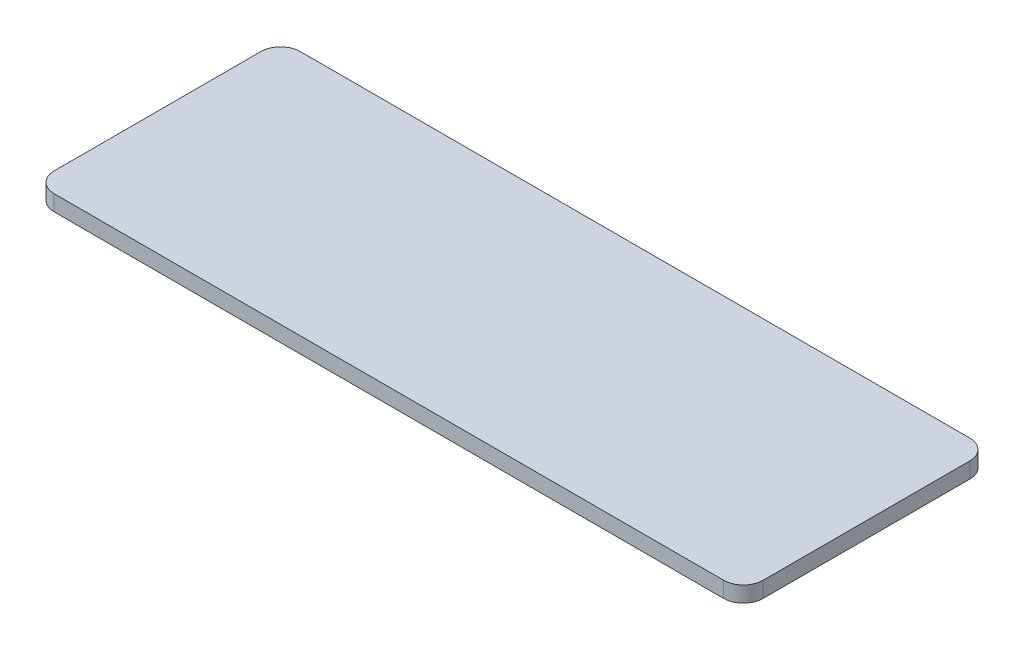
SolidWorks part; units mm, degrees
ref_plane "Front Plane" through (0, 0, 0) normal (0, 0, 1) x (1, 0, 0)
ref_plane "Top Plane" through (0, 0, 0) normal (0, 1, 0) x (1, 0, 0)
ref_plane "Right Plane" through (0, 0, 0) normal (1, 0, 0) x (0, 0, -1)
sketch "Sketch1" plane through (0, 0, 0) normal (0, 1, 0) x (1, 0, 0)
  line L1 (0, 0) -> (72, 0)
  line L2 (0, 0) -> (0, 25)
  line L3 (0, 25) -> (72, 25)
  line L4 (72, 0) -> (72, 25)
  dimension "D1" = 72
  dimension "D2" = 25
extrude "Boss-Extrude1" add sketch "Sketch1" along normal blind 1.6
fillet "Fillet1" radius 2 4 edges at (0, 0.8, 0) (0, 0.8, -25) (72, 0.8, -25) (72, 0.8, 0)
sketch "Sketch2" plane through (0, 1.6, 0) normal (0, 1, 0) x (1, 0, 0)
  line L0 (70, 25) -> (2, 25) construction
  line L1 (72, 2) -> (72, 23) construction
  circle A0 centre (64, 18) radius 0.1
  circle A1 centre (46, 18) radius 0.1
  circle A2 centre (28, 18) radius 0.1
  circle A3 centre (10, 18) radius 0.1
  point P0 (64, 18)
  dimension "D2" = 7
  dimension "D3" = 8
  dimension "D1" = 4
